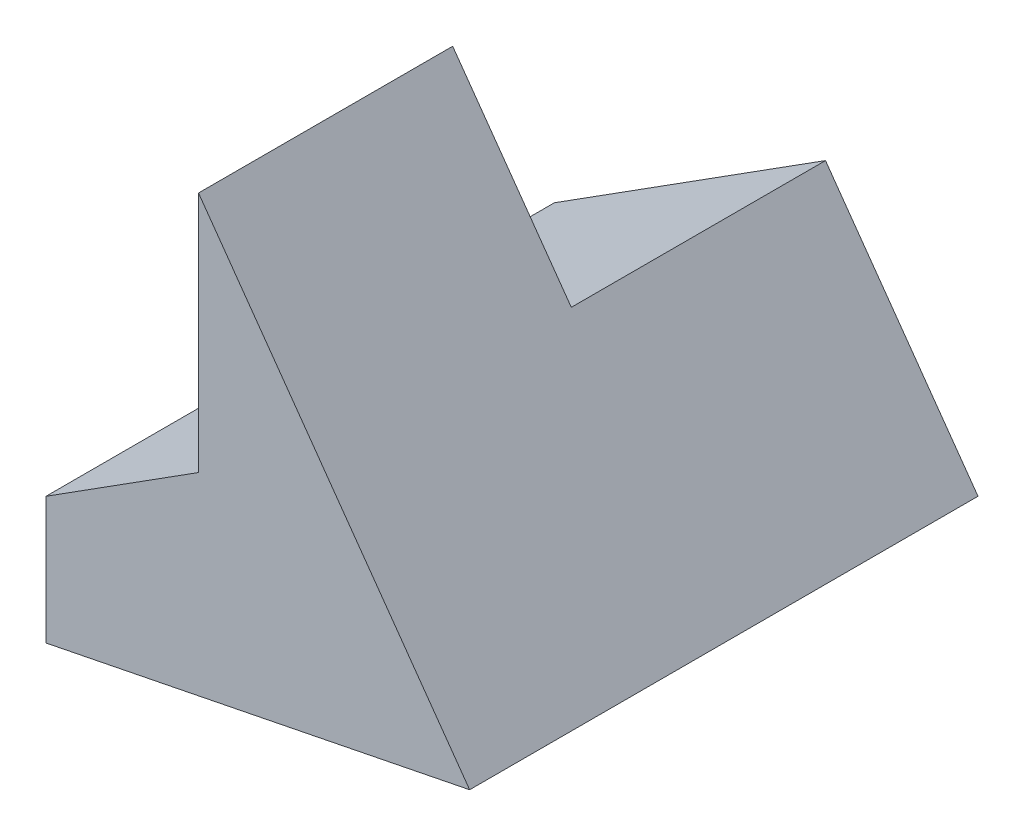
SolidWorks part; units mm, degrees
ref_plane "Front Plane" through (0, 0, 0) normal (0, 0, 1) x (1, 0, 0)
ref_plane "Top Plane" through (0, 0, 0) normal (0, 1, 0) x (1, 0, 0)
ref_plane "Right Plane" through (0, 0, 0) normal (1, 0, 0) x (0, 0, -1)
sketch "Sketch1" plane through (0, 0, 0) normal (0, 0, 1) x (1, 0, 0)
  line L0 (0, 0) -> (5, 1)
  line L2 (5, 1) -> (1.8, 5.5)
  line L3 (1.8, 5.5) -> (1.8, 1.5)
  line L4 (1.8, 1.5) -> (0, 1.5)
  line L5 (0, 1.5) -> (0, 0)
  dimension "D1" = 1
  dimension "D2" = 5
  dimension "D3" = 4
  dimension "D4" = 3.2
  dimension "D5" = 1.5
extrude "Boss-Extrude1" add sketch "Sketch1" along normal blind 3
sketch "Sketch2" plane through (0, 0, 0) normal (0, 0, -1) x (-1, 0, 0)
  line L0 (-5, 1) -> (-3.2, 3.5312)
  line L1 (-5, 1) -> (-1.8, 5.5) construction
  line L2 (-3.2, 3.5312) -> (-3.2, 1.5)
  line L3 (-3.2, 1.5) -> (0, 1.5)
  line L4 (0, 1.5) -> (0, 0)
  line L5 (0, 0) -> (-5, 1)
  dimension "D1" = 3.2
extrude "Boss-Extrude2" add sketch "Sketch2" along normal blind 3
sketch "Sketch3" plane through (0, 0, -3) normal (0, 0, -1) x (-1, 0, 0)
  line L0 (-3.2, 3.5312) -> (0, 1.5)
  line L1 (0, 1.5) -> (-3.2, 1.5)
  line L2 (-3.2, 1.5) -> (-3.2, 3.5312)
extrude "Boss-Extrude3" add sketch "Sketch3" against normal blind 3
sketch "Sketch4" plane through (0, 0, 0) normal (0, 0, 1) x (1, 0, 0)
  line L0 (1.8, 2.6426) -> (1.8, 1.5)
  line L1 (1.8, 1.5) -> (0, 1.5)
  line L2 (0, 1.5) -> (1.8, 2.6426)
extrude "Boss-Extrude4" add sketch "Sketch4" along normal blind 3
